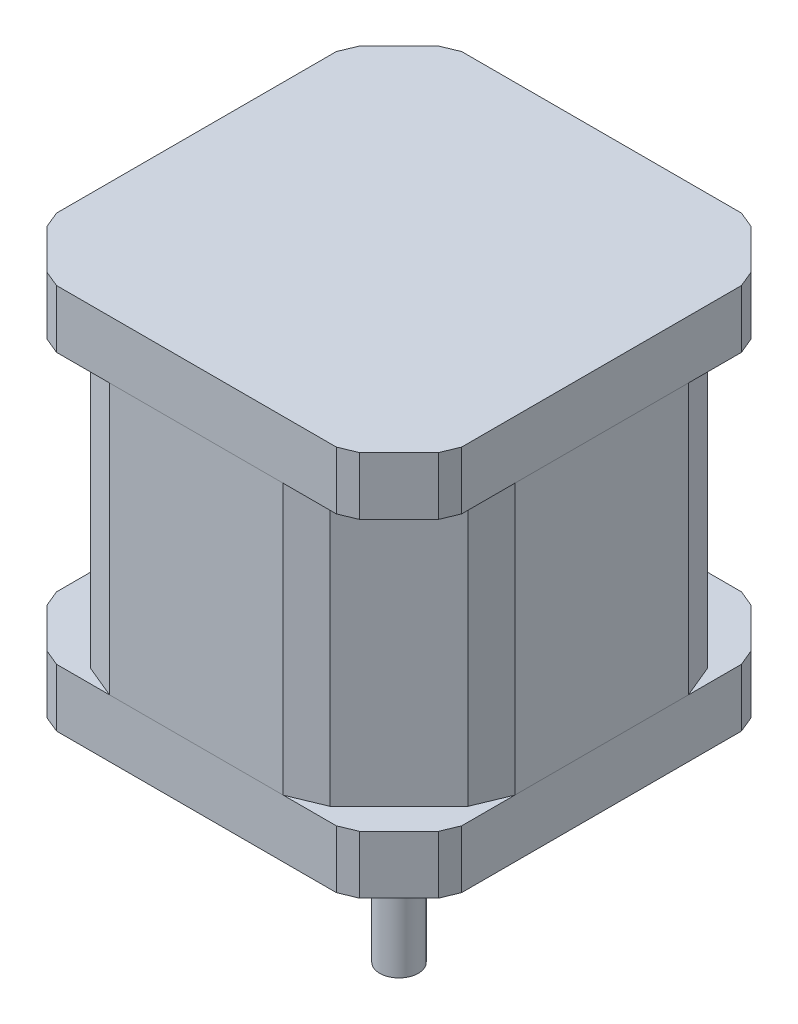
SolidWorks part; units mm, degrees
ref_plane "前视基准面" through (0, 0, 0) normal (0, 0, 1) x (1, 0, 0)
ref_plane "上视基准面" through (0, 0, 0) normal (0, 1, 0) x (1, 0, 0)
ref_plane "右视基准面" through (0, 0, 0) normal (1, 0, 0) x (0, 0, -1)
sketch "草图1" plane through (0, 0, 0) normal (0, 1, 0) x (1, 0, 0)
  line L0 (0, 0) -> (42, 0)
  line L1 (0, 0) -> (0, 42)
  line L2 (42, 0) -> (42, 42)
  line L3 (0, 42) -> (42, 42)
extrude "凸台-拉伸1" add sketch "草图1" along normal blind 6
chamfer "倒角1" distance 5.5 angle 45 4 edges at (0, 3, -42) (42, 3, -42) (42, 3, 0) (0, 3, 0)
sketch "草图2" plane through (0, 0, 0) normal (0, 1, 0) x (1, 0, 0)
  line L0 (0, 0) -> (0, 42)
  line L1 (0, 0) -> (42, 0)
  line L2 (0, 42) -> (42, 42)
  line L3 (42, 0) -> (42, 42)
  line L4 (0, 36.5) -> (0, 5.5) construction
extrude "凸台-拉伸3" add sketch "草图2" against normal blind 28 separate body
chamfer "倒角3" distance 10 angle 45 4 edges at (42, -14, -42) (42, -14, 0) (0, -14, 0) (0, -14, -42)
chamfer "倒角4" distance 2 distance2 2 8 edges at (0, -14, -10) (0, -14, -32) (10, -14, 0) (32, -14, 0) (42, -14, -10) (42, -14, -32) (10, -14, -42) (32, -14, -42)
ref_plane "基准面2" through (0, -28, 0) normal (0, -1, 0) x (-1, 0, 0)
sketch "草图4" plane through (0, -28, 0) normal (0, -1, 0) x (-1, 0, 0)
  line L0 (0, 0) -> (-42, 0)
  line L1 (0, 0) -> (0, 42)
  line L2 (-42, 0) -> (-42, 42)
  line L3 (0, 42) -> (-42, 42)
  line L4 (-12, 0) -> (-30, 0) construction
extrude "凸台-拉伸6" add sketch "草图4" along normal blind 6 separate body
chamfer "倒角5" distance 5.5 angle 45 4 edges at (0, -31, 0) (42, -31, 0) (0, -31, -42) (42, -31, -42)
chamfer "倒角6" distance 1 distance2 1 8 edges at (5.5, -31, 0) (0, -31, -5.5) (0, -31, -36.5) (5.5, -31, -42) (36.5, -31, -42) (42, -31, -36.5) (42, -31, -5.5) (36.5, -31, 0)
chamfer "倒角7" distance 1 distance2 1 8 edges at (36.5, 3, -42) (42, 3, -36.5) (42, 3, -5.5) (36.5, 3, 0) (0, 3, -5.5) (5.5, 3, 0) (0, 3, -36.5) (5.5, 3, -42)
ref_plane "基准面3" through (0, -34, 0) normal (0, -1, 0) x (-1, 0, 0)
sketch "草图5" plane through (0, -34, 0) normal (0, -1, 0) x (-1, 0, 0)
  circle A0 centre (-5.5, 5.5) radius 1.5
  circle A1 centre (-36.5, 5.5) radius 1.5
  circle A2 centre (-36.5, 36.5) radius 1.5
  circle A3 centre (-5.5, 36.5) radius 1.5
extrude "切除-拉伸1" cut sketch "草图5" against normal blind 5
sketch "草图6" plane through (0, -34, 0) normal (0, -1, 0) x (-1, 0, 0)
  circle A0 centre (-21, 21) radius 11
extrude "凸台-拉伸7" add sketch "草图6" along normal blind 1.5
ref_plane "基准面4" through (0, -35.5, 0) normal (0, -1, 0) x (-1, 0, 0)
sketch "草图7" plane through (0, -35.5, 0) normal (0, -1, 0) x (-1, 0, 0)
  circle A0 centre (-21, 21) radius 2
extrude "凸台-拉伸8" add sketch "草图7" along normal blind 22.5
